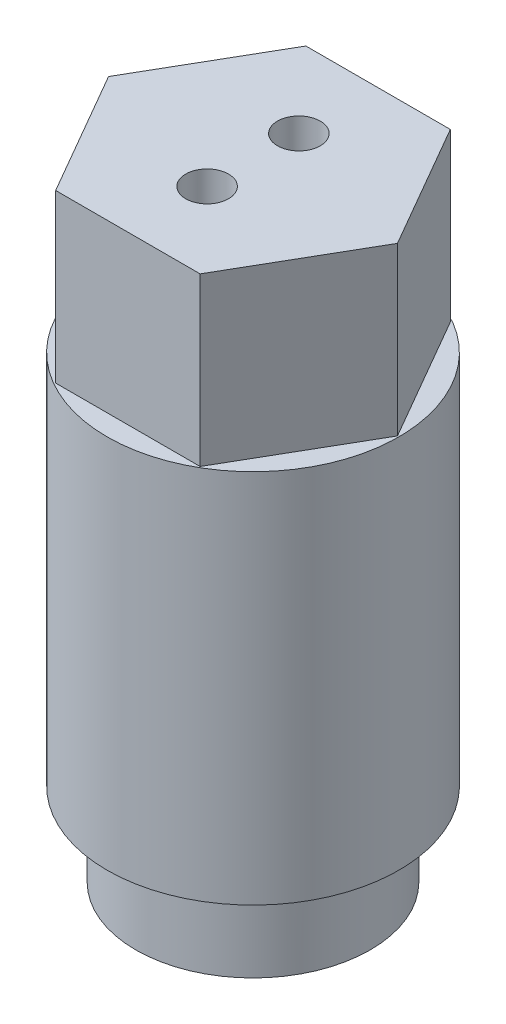
SolidWorks part; units mm, degrees
material "6061-T6 (SS)"
ref_plane "Front Plane" through (0, 0, 0) normal (0, 0, 1) x (1, 0, 0)
ref_plane "Top Plane" through (0, 0, 0) normal (0, 1, 0) x (1, 0, 0)
ref_plane "Right Plane" through (0, 0, 0) normal (1, 0, 0) x (0, 0, -1)
sketch "Main Body Profile" plane through (0, 0, 0) normal (0, 1, 0) x (1, 0, 0)
  circle A0 centre (0, 0) radius 11.1125
  dimension "D1" = 22.225
extrude "Main Body Extrude" add sketch "Main Body Profile" along normal blind 28.575 contours A0
sketch "Hexagon Profile" plane through (0, 28.575, 0) normal (0, 1, 0) x (1, 0, 0)
  line L1 (5.4993, 9.525) -> (-5.4993, 9.525)
  line L2 (-5.4993, 9.525) -> (-10.9985, 0)
  line L3 (-10.9985, 0) -> (-5.4993, -9.525)
  line L4 (-5.4993, -9.525) -> (5.4993, -9.525)
  line L5 (5.4993, -9.525) -> (10.9985, 0)
  line L6 (10.9985, 0) -> (5.4993, 9.525)
  circle A0 centre (0, 0) radius 9.525 construction
  dimension "D1" = 19.05
extrude "Hexagon Body" add sketch "Hexagon Profile" along normal blind 12.7
sketch "Tip Profile" plane through (0, 0, 0) normal (0, -1, 0) x (1, 0, 0)
  circle A0 centre (0, 0) radius 8.9281
  dimension "D1" = 17.8562
extrude "Tip Body" add sketch "Tip Profile" along normal blind 6.35
sketch "Reference Sketch" plane through (0, -6.35, 0) normal (0, -1, 0) x (1, 0, 0)
  circle A0 centre (0, 0) radius 6.35
  dimension "D1" = 12.7
hole_wizard "Back Powder Hole" positions "Sketch9" profile "Sketch8" hole size "1/2" standard "ANSI Inch"
sketch "Sketch9" plane through (0, -6.35, 0) normal (0, -1, 0) x (-1, 0, 0)
  point P0 (0, 0)
sketch "Sketch8" plane through (0, -6.35, 0) normal (1, 0, 0) x (0, 0, -1)
  line L0 (0, 0) -> (0, 34.925)
  line L1 (0, 34.925) -> (6.35, 31.1095)
  line L2 (6.35, 31.1095) -> (6.35, 0)
  line L5 (6.35, 0) -> (0, 0)
  line L10 (0, 34.925) -> (-6.35, 31.1095) construction
  line L11 (0, -6.35) -> (0, 107.95) construction
  dimension "Hole Dia." = 12.7
  dimension "Hole Depth" = 34.925
  dimension "Drill Angle" = 118
ref_plane "Countersink Plane" through (0, 33.8966, 0) normal (0, 1, 0) x (1, 0, 0)
sketch "Sketch5" plane through (0, 33.8966, 0) normal (0, 1, 0) x (1, 0, 0)
  line L0 (0, 9.525) -> (0, -9.525) construction
  line L2 (5.4993, 9.525) -> (-5.4993, 9.525) construction
  line L3 (-5.4993, -9.525) -> (5.4993, -9.525) construction
  circle A1 centre (0, 3.4925) radius 1.7463
  circle A2 centre (0, -3.4925) radius 1.7462
  point P8 (0, 3.4925)
  point P10 (0, -3.4925)
  dimension "D1" = 3.4925
  dimension "D3" = 3.4925
  dimension "D2" = 3.4925
hole_wizard "Screw Holes" positions "Sketch5" profile "Sketch11" countersink size "#4" standard "ANSI Inch"
sketch "Sketch11" plane through (0, 33.8966, 3.4925) normal (1, 0, 0) x (0, 0, -1)
  line L0 (0, 0) -> (0, 7.3784)
  line L1 (0, 7.3784) -> (1.6319, 7.3784)
  line L2 (1.6319, 7.3784) -> (1.6319, 1.0284)
  line L3 (1.6319, 1.0284) -> (2.8575, 0)
  line L5 (2.8575, 0) -> (0, 0)
  line L6 (-1.6319, 1.0284) -> (-2.8575, 0) construction
  line L11 (0, -6.35) -> (0, 107.95) construction
  dimension "Thru Hole Dia." = 3.2639
  dimension "Thru Hole Depth" = 7.3784
  dimension "Near C'Sink Dia." = 5.715
  dimension "Near C'Sink Angle" = 100
sketch "Sketch12" plane through (0, 33.8966, 0) normal (0, 1, 0) x (1, 0, 0)
  circle A0 centre (0, 3.4925) radius 2.8575
  circle A1 centre (0, -3.4925) radius 2.8575
  circle A2 centre (0, 0) radius 6.35 construction
extrude "Through Holes" cut sketch "Sketch12" against normal through all
sketch "Sketch13" plane through (0, 0, 0) normal (0, 0, 1) x (1, 0, 0)
  line L0 (0, 0) -> (0, -6.35) construction
  line L1 (-6.35, -6.35) -> (6.35, -6.35) construction
  line L2 (-8.9281, 0) -> (-7.6962, 0)
  line L3 (-8.9281, 0) -> (8.9281, 0) construction
  line L4 (-7.6962, 0) -> (-8.9281, -0.7112)
  line L5 (-8.9281, 0) -> (-8.9281, -6.35) construction
  line L6 (-8.9281, -0.7112) -> (-8.9281, 0)
  dimension "D1" = 0.7112
  dimension "D2" = 1.4225
revolve "Revolved Cut" cut sketch "Sketch13" angle 360 about L0
